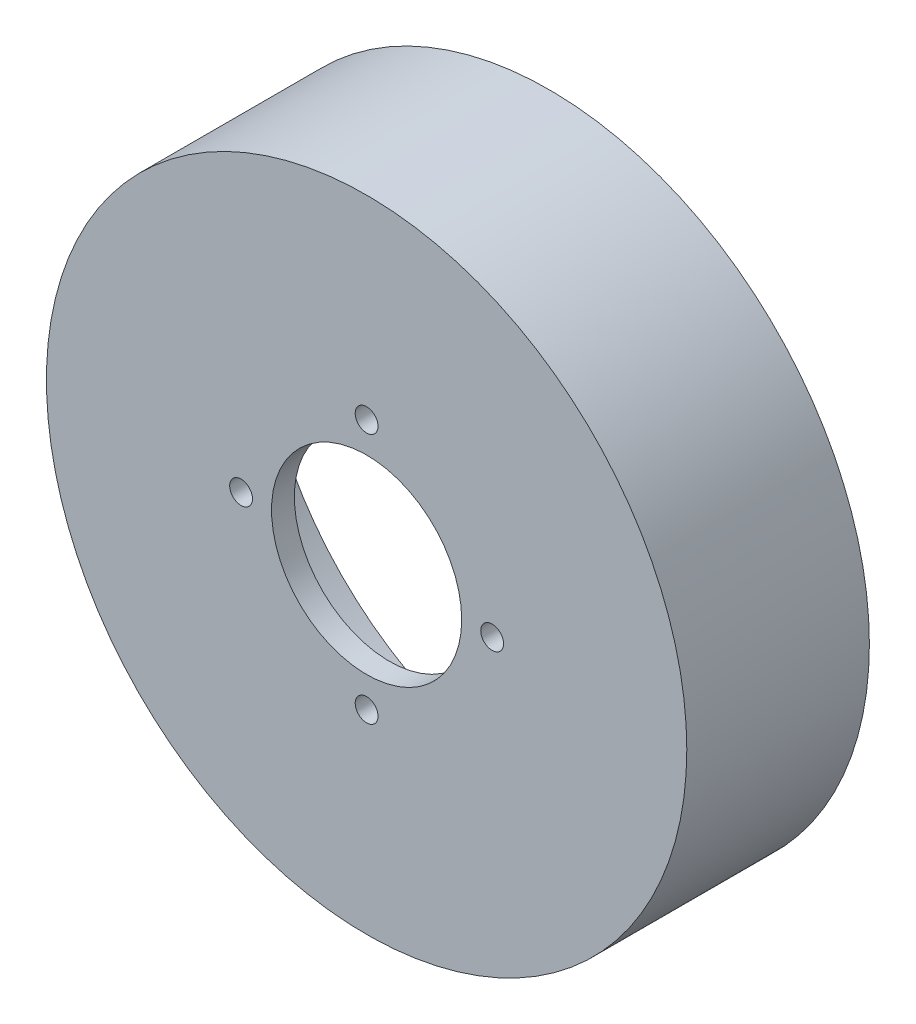
SolidWorks part; units mm, degrees
ref_plane "Front Plane" through (0, 0, 0) normal (0, 0, 1) x (1, 0, 0)
ref_plane "Top Plane" through (0, 0, 0) normal (0, 1, 0) x (1, 0, 0)
ref_plane "Right Plane" through (0, 0, 0) normal (1, 0, 0) x (0, 0, -1)
sketch "Sketch1" plane through (0, 0, -8) normal (0, 0, 1) x (1, 0, 0)
  circle A0 centre (0, 0) radius 38.0875 construction
  circle A1 centre (0, 0) radius 38.0875 construction
  circle A2 centre (0, 0) radius 42.0875
extrude "Boss-Extrude1" add sketch "Sketch1" along normal blind 24
sketch "Sketch2" plane through (0, 0, -8) normal (0, 0, -1) x (-1, 0, 0)
  circle A0 centre (0, 0) radius 38.2875
extrude "Cut-Extrude1" cut sketch "Sketch2" against normal offset from surface (11 mm away) 13 up to face at (42.0875, 0, 16)
sketch "Sketch3" plane through (0, 0, 3) normal (0, 0, -1) x (-1, 0, 0)
  circle A0 centre (0, 0) radius 34.2875
extrude "Cut-Extrude2" cut sketch "Sketch3" against normal offset from surface (10 mm away) 3 up to face at (42.0875, 0, 16)
sketch "Sketch5" plane through (0, 0, 16) normal (0, 0, 1) x (1, 0, 0)
  circle A0 centre (0, 0) radius 12.5
  point P7 (-8.8388, 8.8388)
  dimension "D1" = 25
extrude "Cut-Extrude4" cut sketch "Sketch5" against normal through all both and the other way through all
sketch "Sketch4" plane through (0, 0, 13) normal (0, 0, -1) x (-1, 0, 0)
  line L0 (0, 0) -> (-45.3422, 0) construction
  circle A0 centre (0, 0) radius 15 construction
  circle A1 centre (-16.5, 0) radius 1.5
  point P7 (-15, 0)
  dimension "D1" = 30
  dimension "D2" = 3
extrude "Cut-Extrude3" cut sketch "Sketch4" against normal through all both and the other way through all
pattern_circular "CirPattern1" count 4 over 360 about axis through (0, 0, 0) along (0, 0, 1) of "Cut-Extrude3"
move or copy body "correct side for 3d printing" [suppressed] bodies to move or copy 105 copy no rotation origin (0, 0, 0.25) rotation axis (0, 1, 0) rotation angle 180
equation "\"circ_spline_outer\"= \"D1@Sketch1\""
equation "\"cup_outer_dia\"= \"circ_spline_outer\" + 8mm"
equation "\"cup_inner_dia\"= \"circ_spline_outer\" + 0.4mm'inside dia + clearance to fit over circ spline"
equation "\"D2@Sketch1\"= \"cup_outer_dia\""
equation "\"base_to_first_bearing_height\"= 13mm'height from the mounting plate of the motor to the first bearing"
equation "\"cup_circ_spline_overlap_height\"= 8mm'height where the motor holding cup fits into the circ spline"
equation "\"motor_holding_plate_height\"= 3mm'back plate of the cup, holding the motor"
equation "\"cup_total_height\"= \"base_to_first_bearing_height\" + \"cup_circ_spline_overlap_height\" + \"motor_holding_plate_height\""
equation "\"D1@Sketch2\"= \"cup_inner_dia\""
equation "\"D1@Sketch3\"= \"cup_inner_dia\" - 8"
